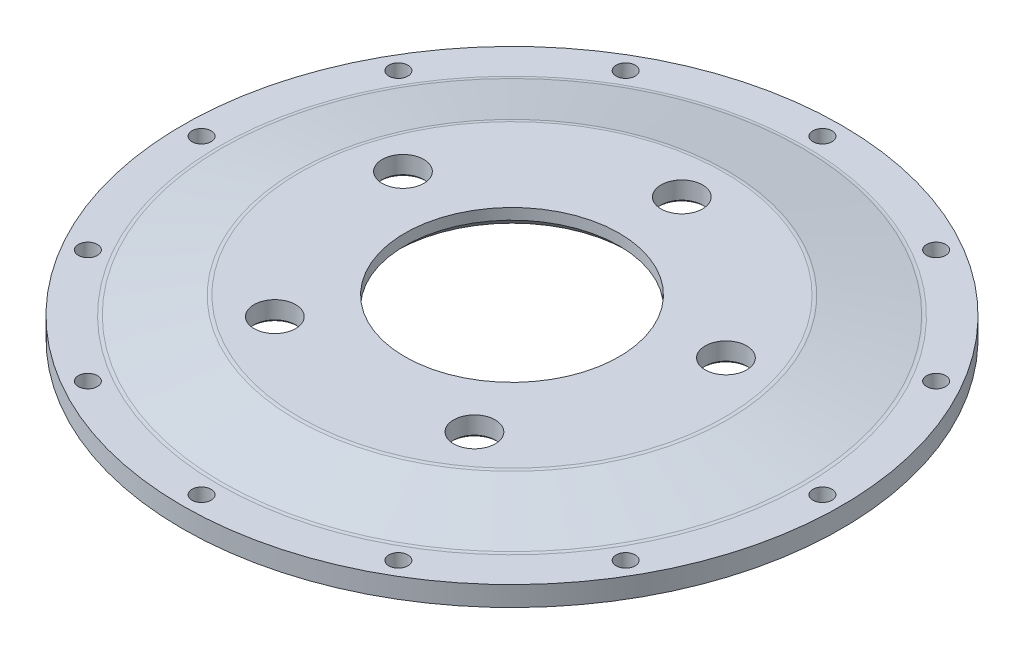
SolidWorks part; units mm, degrees
material "7075-T6 (SN)"
ref_plane "Front Plane" through (0, 0, 0) normal (0, 0, 1) x (1, 0, 0)
ref_plane "Top Plane" through (0, 0, 0) normal (0, 1, 0) x (1, 0, 0)
ref_plane "Right Plane" through (0, 0, 0) normal (1, 0, 0) x (0, 0, -1)
sketch "Sketch1" plane through (0, 0, 0) normal (0, 1, 0) x (1, 0, 0)
  line L0 (0, 118.5349) -> (0, -119.9893) construction
  line L1 (-24.3339, 110.925) -> (25.0755, 110.925) construction
  line L2 (25.0755, 98.075) -> (-24.3339, 98.075) construction
  circle A0 centre (0, 0) radius 110.925
  circle A1 centre (0, 104.5) radius 3.2125
  circle A2 centre (0, 0) radius 98.075
  circle A3 centre (52.25, 90.4997) radius 3.2125
  circle A4 centre (90.4997, 52.25) radius 3.2125
  circle A5 centre (104.5, 0) radius 3.2125
  circle A6 centre (90.4997, -52.25) radius 3.2125
  circle A7 centre (52.25, -90.4997) radius 3.2125
  circle A8 centre (0, -104.5) radius 3.2125
  circle A9 centre (-52.25, -90.4997) radius 3.2125
  circle A10 centre (-90.4997, -52.25) radius 3.2125
  circle A11 centre (-104.5, 0) radius 3.2125
  circle A12 centre (0, 0) radius 104.5 construction
  circle A13 centre (-90.4997, 52.25) radius 3.2125
  circle A14 centre (-52.25, 90.4997) radius 3.2125
  point P28 (0, 0)
  point P33 (0, 0)
  point P35 (0, 0)
  point P37 (0, 0)
  point P42 (0, 0)
  dimension "D1" = 6.425
  dimension "D4" = 209
  dimension "D3" = 12.85
  dimension "D5" = 6.425
  dimension "D2" = 12
extrude "Boss-Extrude1" add sketch "Sketch1" along normal blind 6.7
ref_plane "Top Of Hat" through (0, 12.7, 0) normal (0, 1, 0) x (1, 0, 0)
sketch "Sketch2" plane through (0, 12.7, 0) normal (0, 1, 0) x (1, 0, 0)
  circle A0 centre (0, 0) radius 72
  circle A1 centre (0, 0) radius 36.055
  circle A2 centre (0, 57.15) radius 7
  circle A3 centre (54.3529, 17.6603) radius 7
  circle A4 centre (33.5919, -46.2353) radius 7
  circle A5 centre (-33.5919, -46.2353) radius 7
  circle A6 centre (-54.3529, 17.6603) radius 7
  point P16 (0, 0)
  dimension "D1" = 144
  dimension "D2" = 72.11
  dimension "D3" = 14
  dimension "D4" = 57.15
  dimension "D5" = 5
extrude "Boss-Extrude3" add sketch "Sketch2" against normal blind 6.7 separate body
sketch "Sketch3" [suppressed] plane through (0, 0, 0) normal (0, 0, 1) x (1, 0, 0)
  line L0 (-73.355, 19.5) -> (-88.8, 6.7)
  line L1 (-88.8, 6.7) -> (-88.8, 0)
  line L3 (-73.355, 12.8) -> (-73.355, 19.5)
  line L4 (-73.355, 19.5) -> (-73.2286, 19.6264)
  line L5 (-88.8, 0) -> (-73.355, 12.8)
  line L6 (-73.355, 19.5) -> (-73.355, 12.8) construction
surface "Surface-Fill7" [suppressed]
surface "Surface-Fill8" [suppressed]
sketch "Sketch4" plane through (0, 0, 0) normal (0, 0, 1) x (1, 0, 0)
  line L0 (72, 12.7) -> (98.075, 6.7)
  line L1 (72, 6) -> (98.075, 0)
  line L2 (-98.075, 0) -> (98.075, 0) construction
  line L4 (98.075, 6.7) -> (98.075, 0)
  line L5 (109.8492, 0) -> (75.9796, 0) construction
  line L7 (72, 6) -> (72, 12.7)
  line L11 (-72, 6) -> (72, 6) construction
sweep "Sweep3" add profiles "Sketch4" path edge at (0, 6, 72)
fillet "Fillet1" radius 5 1 edges at (0, 12.7, 72)
fillet "Fillet2" radius 5 1 edges at (0, 6.7, 98.075)
chamfer "Chamfer1" distance 3 angle 45 1 edges at (0, 6, 36.055)
chamfer "Chamfer2" distance 0.8 angle 45 5 edges at (0, 6, -50.15) (54.3529, 6, -10.6603) (33.5919, 6, 53.2353) (-33.5919, 6, 53.2353) (-54.3529, 6, -10.6603)
fillet "Fillet7" radius 2.5 1 edges at (0, 6, -72)
fillet "Fillet8" radius 2.5 1 edges at (0, 0, -98.075)
equation "\"D3@Sketch1\"=\"D1@Sketch1\"*2"
equation "\"D5@Sketch1\"=\"D3@Sketch1\"/2"
